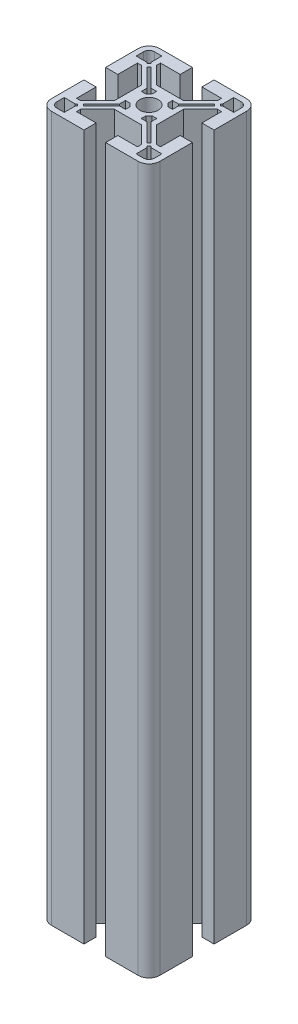
SolidWorks part; units mm, degrees
ref_plane "Ebene vorne" through (0, 0, 0) normal (0, 0, 1) x (1, 0, 0)
ref_plane "Ebene oben" through (0, 0, 0) normal (0, 1, 0) x (1, 0, 0)
ref_plane "Ebene rechts" through (0, 0, 0) normal (1, 0, 0) x (0, 0, -1)
sketch "Sketch1" plane through (0, 0, 0) normal (0, 1, 0) x (1, 0, 0)
  line L0 (-7.9326, -10.8599) -> (-58.869, -10.8599) construction
  line L1 (-7.9326, -10.8599) -> (-7.9326, 43.7859) construction
  line L2 (-7.9326, -10.8599) -> (-62.5783, 43.7859) construction
  line L3 (-27.9326, -6.8599) -> (-27.9326, 5.1401)
  line L4 (-27.9326, -6.8599) -> (-23.4326, -6.8599)
  line L5 (-23.4326, -6.8599) -> (-23.4326, 0.3901)
  line L6 (-23.4326, 0.3901) -> (-21.9326, 0.3901)
  line L7 (-21.9326, 0.3901) -> (-15.6826, -5.8599)
  line L8 (-15.6826, -5.8599) -> (-15.6826, -10.8599)
  line L9 (-25.9326, 2.3901) -> (-25.9326, 5.1401)
  line L10 (-25.9326, 2.3901) -> (-21.8897, 2.3901)
  line L11 (-21.4415, 1.9419) -> (-20.7344, 2.649)
  line L12 (-21.4415, 1.9419) -> (-21.8897, 2.3901)
  line L13 (-20.3808, 0.8813) -> (-13.6826, -5.817)
  line L14 (-13.6826, -5.817) -> (-13.6826, -7.9551)
  line L15 (-20.3808, 0.8813) -> (-19.6737, 1.5884)
  line L16 (-13.6826, -7.9551) -> (-13.1826, -7.9551)
  line L17 (-19.6737, 1.5884) -> (-12.9755, -5.1099)
  line L18 (-10.8374, -5.1099) -> (-10.8374, -5.6099)
  line L19 (-12.9755, -5.1099) -> (-10.8374, -5.1099)
  line L20 (-21.1826, 7.1401) -> (-21.1826, 3.0973)
  line L21 (-21.1826, 7.1401) -> (-23.9326, 7.1401)
  line L22 (-19.1826, 3.1401) -> (-12.9326, -3.1099)
  line L23 (-11.9326, 9.1401) -> (-11.9326, 4.6401)
  line L24 (-19.1826, 4.6401) -> (-19.1826, 3.1401)
  line L25 (-12.9326, -3.1099) -> (-7.9326, -3.1099)
  line L26 (-11.9326, 4.6401) -> (-19.1826, 4.6401)
  line L27 (-11.9326, 9.1401) -> (-23.9326, 9.1401)
  line L28 (7.5674, -6.8599) -> (7.5674, 0.3901)
  line L29 (12.0674, -6.8599) -> (12.0674, 5.1401)
  line L30 (12.0674, -6.8599) -> (7.5674, -6.8599)
  line L31 (10.0674, 2.3901) -> (10.0674, 5.1401)
  line L32 (10.0674, 2.3901) -> (6.0245, 2.3901)
  line L33 (6.0674, 0.3901) -> (-0.1826, -5.8599)
  line L34 (7.5674, 0.3901) -> (6.0674, 0.3901)
  line L35 (-0.1826, -5.8599) -> (-0.1826, -10.8599)
  line L36 (-2.1826, -5.817) -> (-2.1826, -7.9551)
  line L37 (3.8085, 1.5884) -> (-2.8897, -5.1099)
  line L38 (4.5156, 0.8813) -> (-2.1826, -5.817)
  line L39 (-2.8897, -5.1099) -> (-5.0279, -5.1099)
  line L40 (-5.0279, -5.1099) -> (-5.0279, -5.6099)
  line L41 (-2.1826, -7.9551) -> (-2.6826, -7.9551)
  line L42 (-2.9326, -3.1099) -> (-7.9326, -3.1099)
  line L43 (3.3174, 3.1401) -> (-2.9326, -3.1099)
  line L44 (5.3174, 7.1401) -> (5.3174, 3.0973)
  line L45 (5.3174, 7.1401) -> (8.0674, 7.1401)
  line L46 (-3.9326, 4.6401) -> (3.3174, 4.6401)
  line L47 (3.3174, 4.6401) -> (3.3174, 3.1401)
  line L48 (-3.9326, 9.1401) -> (8.0674, 9.1401)
  line L49 (-3.9326, 9.1401) -> (-3.9326, 4.6401)
  line L50 (-3.9326, -26.3599) -> (3.3174, -26.3599)
  line L51 (-3.9326, -30.8599) -> (8.0674, -30.8599)
  line L52 (-3.9326, -30.8599) -> (-3.9326, -26.3599)
  line L53 (5.3174, -28.8599) -> (8.0674, -28.8599)
  line L54 (5.3174, -28.8599) -> (5.3174, -24.817)
  line L55 (3.3174, -24.8599) -> (-2.9326, -18.6099)
  line L56 (3.3174, -26.3599) -> (3.3174, -24.8599)
  line L57 (-2.9326, -18.6099) -> (-7.9326, -18.6099)
  line L58 (-2.8897, -16.6099) -> (-5.0279, -16.6099)
  line L59 (4.5156, -22.601) -> (-2.1826, -15.9027)
  line L60 (3.8085, -23.3081) -> (-2.8897, -16.6099)
  line L61 (-2.1826, -15.9027) -> (-2.1826, -13.7646)
  line L62 (-2.1826, -13.7646) -> (-2.6826, -13.7646)
  line L63 (-5.0279, -16.6099) -> (-5.0279, -16.1099)
  line L64 (-0.1826, -15.8599) -> (-0.1826, -10.8599)
  line L65 (6.0674, -22.1099) -> (-0.1826, -15.8599)
  line L66 (10.0674, -24.1099) -> (6.0245, -24.1099)
  line L67 (10.0674, -24.1099) -> (10.0674, -26.8599)
  line L68 (7.5674, -14.8599) -> (7.5674, -22.1099)
  line L69 (7.5674, -22.1099) -> (6.0674, -22.1099)
  line L70 (12.0674, -14.8599) -> (12.0674, -26.8599)
  line L71 (12.0674, -14.8599) -> (7.5674, -14.8599)
  line L72 (-23.4326, -14.8599) -> (-23.4326, -22.1099)
  line L73 (-27.9326, -14.8599) -> (-27.9326, -26.8599)
  line L74 (-27.9326, -14.8599) -> (-23.4326, -14.8599)
  line L75 (-25.9326, -24.1099) -> (-25.9326, -26.8599)
  line L76 (-25.9326, -24.1099) -> (-21.8897, -24.1099)
  line L77 (-21.9326, -22.1099) -> (-15.6826, -15.8599)
  line L78 (-23.4326, -22.1099) -> (-21.9326, -22.1099)
  line L79 (-15.6826, -15.8599) -> (-15.6826, -10.8599)
  line L80 (-13.6826, -15.9027) -> (-13.6826, -13.7646)
  line L81 (-19.6737, -23.3081) -> (-12.9755, -16.6099)
  line L82 (-20.3808, -22.601) -> (-13.6826, -15.9027)
  line L83 (-12.9755, -16.6099) -> (-10.8374, -16.6099)
  line L84 (-10.8374, -16.6099) -> (-10.8374, -16.1099)
  line L85 (-13.6826, -13.7646) -> (-13.1826, -13.7646)
  line L86 (-12.9326, -18.6099) -> (-7.9326, -18.6099)
  line L87 (-19.1826, -24.8599) -> (-12.9326, -18.6099)
  line L88 (-21.1826, -28.8599) -> (-21.1826, -24.817)
  line L89 (-21.1826, -28.8599) -> (-23.9326, -28.8599)
  line L90 (-11.9326, -26.3599) -> (-19.1826, -26.3599)
  line L91 (-19.1826, -26.3599) -> (-19.1826, -24.8599)
  line L92 (-11.9326, -30.8599) -> (-23.9326, -30.8599)
  line L93 (-11.9326, -30.8599) -> (-11.9326, -26.3599)
  line L94 (-20.7344, 2.649) -> (-21.1826, 3.0973)
  line L95 (4.8692, 2.649) -> (5.3174, 3.0973)
  line L96 (4.8692, 2.649) -> (5.5763, 1.9419)
  line L97 (5.5763, 1.9419) -> (6.0245, 2.3901)
  line L98 (3.8085, 1.5884) -> (4.5156, 0.8813)
  line L99 (5.5763, -23.6616) -> (6.0245, -24.1099)
  line L100 (5.5763, -23.6616) -> (4.8692, -24.3687)
  line L101 (4.8692, -24.3687) -> (5.3174, -24.817)
  line L102 (4.5156, -22.601) -> (3.8085, -23.3081)
  line L103 (-20.7344, -24.3687) -> (-21.1826, -24.817)
  line L104 (-20.7344, -24.3687) -> (-21.4415, -23.6616)
  line L105 (-21.4415, -23.6616) -> (-21.8897, -24.1099)
  line L106 (-19.6737, -23.3081) -> (-20.3808, -22.601)
  line L107 (-13.1826, -7.9551) -> (-12.0023, -7.9551)
  line L108 (-10.8374, -5.6099) -> (-10.8374, -6.7901)
  line L109 (-5.0279, -5.6099) -> (-5.0279, -6.7901)
  line L110 (-2.6826, -7.9551) -> (-3.8629, -7.9551)
  line L111 (-2.6826, -13.7646) -> (-3.8629, -13.7646)
  line L112 (-5.0279, -16.1099) -> (-5.0279, -14.9296)
  line L113 (-10.8374, -16.1099) -> (-10.8374, -14.9296)
  line L114 (-13.1826, -13.7646) -> (-12.0023, -13.7646)
  arc A0 (-27.9326, 5.1401) -> (-23.9326, 9.1401) centre (-23.9326, 5.1401) cw
  arc A1 (-25.9326, 5.1401) -> (-23.9326, 7.1401) centre (-23.9326, 5.1401) cw
  arc A2 (-11.3326, -10.8599) -> (-7.9326, -7.4599) centre (-7.9326, -10.8599) cw
  arc A3 (-12.0023, -13.7646) -> (-10.8374, -14.9296) centre (-7.9326, -10.8599) ccw
  arc A4 (8.0674, 9.1401) -> (12.0674, 5.1401) centre (8.0674, 5.1401) cw
  arc A5 (8.0674, 7.1401) -> (10.0674, 5.1401) centre (8.0674, 5.1401) cw
  arc A6 (-5.0279, -14.9296) -> (-3.8629, -13.7646) centre (-7.9326, -10.8599) ccw
  arc A7 (-7.9326, -7.4599) -> (-4.5326, -10.8599) centre (-7.9326, -10.8599) cw
  arc A8 (12.0674, -26.8599) -> (8.0674, -30.8599) centre (8.0674, -26.8599) cw
  arc A9 (10.0674, -26.8599) -> (8.0674, -28.8599) centre (8.0674, -26.8599) cw
  arc A10 (-3.8629, -7.9551) -> (-5.0279, -6.7901) centre (-7.9326, -10.8599) ccw
  arc A11 (-4.5326, -10.8599) -> (-7.9326, -14.2599) centre (-7.9326, -10.8599) cw
  arc A12 (-23.9326, -30.8599) -> (-27.9326, -26.8599) centre (-23.9326, -26.8599) cw
  arc A13 (-23.9326, -28.8599) -> (-25.9326, -26.8599) centre (-23.9326, -26.8599) cw
  arc A14 (-10.8374, -6.7901) -> (-12.0023, -7.9551) centre (-7.9326, -10.8599) ccw
  arc A15 (-7.9326, -14.2599) -> (-11.3326, -10.8599) centre (-7.9326, -10.8599) cw
  point P19 (-20.0273, 1.2348)
  point P41 (-21.0879, 2.2955)
  point P140 (-7.9326, -10.8599)
  point P149 (-7.9326, -10.8599)
  point P152 (-7.9326, -10.8599)
extrude "Boss-Extrude1" add sketch "Sketch1" along normal mid plane 260 contours A12 L92 L93 L90 L91 L87 L86 L57 L55 L56 L50 L52 L51 A8 L70 L71 L68 L69 L65 L64 L35 L33 L34 L28 L30 L29 A4 L48 L49 L46 L47 L43 L42 L25 L22 L24 L26 L23 L27 A0 L3 L4 L5 L6 L7 L8 L79 L77 L78 L72 L74
